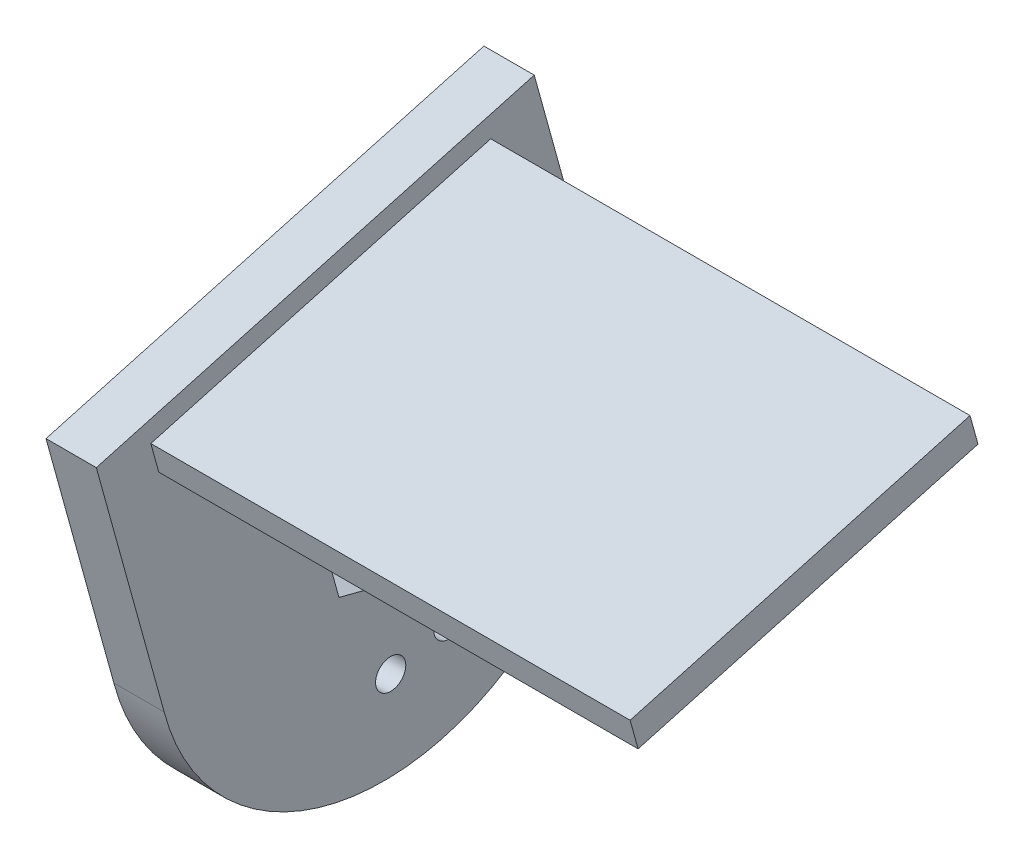
SolidWorks part; units mm, degrees
ref_plane "Front Plane" through (0, 0, 0) normal (0, 0, 1) x (1, 0, 0)
ref_plane "Top Plane" through (0, 0, 0) normal (0, 1, 0) x (1, 0, 0)
ref_plane "Right Plane" through (0, 0, 0) normal (1, 0, 0) x (0, 0, -1)
sketch "Sketch1" plane through (0, 0, 0) normal (1, 0, 0) x (0, 0, -1)
  circle A0 centre (0, 0) radius 22.57
  dimension "D1" = 45.14
extrude "Boss-Extrude1" add sketch "Sketch1" along normal blind 5
sketch "Sketch3" plane through (5, 0, 0) normal (1, 0, 0) x (0, 0, -1)
  line L0 (21.8337, 5.7178) -> (14.931, 30.7011)
  line L1 (14.931, 30.7011) -> (-28.5749, 18.6807)
  line L2 (-28.5749, 18.6807) -> (-21.8337, -5.7178)
  line L3 (21.8337, 5.7178) -> (-21.8337, -5.7178)
  line L4 (-21.7529, -6.0102) -> (-28.5749, 18.6807) construction
  line L5 (14.931, 30.7011) -> (21.7529, 6.0102) construction
  circle A1 centre (0, 0) radius 22.57 construction
extrude "Boss-Extrude2" add sketch "Sketch3" against normal blind 5
sketch "Sketch4" plane through (0, 0, 0) normal (-1, 0, 0) x (0, 0, 1)
  line L0 (-1.5433, -5.5857) -> (4.0657, -4.1294) construction
  line L1 (4.0657, -4.1294) -> (5.609, 1.4563) construction
  line L2 (5.609, 1.4563) -> (1.5433, 5.5857) construction
  line L3 (1.5433, 5.5857) -> (-4.0657, 4.1294) construction
  line L4 (-4.0657, 4.1294) -> (-5.609, -1.4563) construction
  line L5 (-5.609, -1.4563) -> (-1.5433, -5.5857) construction
  line L6 (-1.5433, -5.5857) -> (4.0657, -4.1294) construction
  line L7 (4.4708, -4.5408) -> (6.1678, 1.6014)
  line L8 (6.1678, 1.6014) -> (1.6971, 6.1422)
  line L9 (1.6971, 6.1422) -> (-4.4708, 4.5408)
  line L10 (-4.4708, 4.5408) -> (-6.1678, -1.6014)
  line L11 (-6.1678, -1.6014) -> (-1.6971, -6.1422)
  line L12 (-1.6971, -6.1422) -> (4.4708, -4.5408)
  circle A0 centre (0, 0) radius 5.0186 construction
  circle A1 centre (0, 0) radius 5.5186 construction
  dimension "D1" = 0.5
  dimension "D2" = 0
extrude "Cut-Extrude2" cut sketch "Sketch4" against normal blind 5
sketch "Sketch5" plane through (5, 0, 0) normal (1, 0, 0) x (0, 0, -1)
  circle A0 centre (0.6693, -13.6872) radius 1.5
  circle A1 centre (6.4526, -12.0893) radius 1.5
extrude "Cut-Extrude3" cut sketch "Sketch5" against normal blind 5
sketch "Sketch6" plane through (5, 0, 0) normal (1, 0, 0) x (0, 0, -1)
  line L0 (10.6442, 27.4418) -> (-23.2228, 18.0845)
  line L5 (-23.2228, 18.0845) -> (-22.4063, 15.1292)
  line L6 (-22.4063, 15.1292) -> (11.4607, 24.4865)
  line L7 (11.4607, 24.4865) -> (-22.4063, 15.1292) construction
  line L8 (10.6442, 27.4418) -> (11.4607, 24.4865) construction
  line L9 (11.4607, 24.4865) -> (10.6442, 27.4418)
extrude "Boss-Extrude3" add sketch "Sketch6" along normal up to surface (47.62 mm away)
sketch "Sketch7" plane through (52.62, 0, 0) normal (1, 0, 0) x (0, 0, -1)
  line L0 (11.3992, 24.5214) -> (10.6093, 27.3803)
  line L1 (10.6093, 27.3803) -> (-23.1613, 18.0496)
  line L2 (-23.1613, 18.0496) -> (-22.3714, 15.1907)
  line L3 (-22.3714, 15.1907) -> (11.3992, 24.5214)
  line L4 (11.4607, 24.4865) -> (-22.4063, 15.1292) construction
  line L5 (-23.2228, 18.0845) -> (10.6442, 27.4418) construction
  line L7 (-22.4063, 15.1292) -> (-23.2228, 18.0845) construction
  line L8 (10.6442, 27.4418) -> (11.4607, 24.4865) construction
  line L9 (11.4607, 24.4865) -> (10.6442, 27.4418)
  line L10 (10.6442, 27.4418) -> (-23.2228, 18.0845)
  line L11 (-23.2228, 18.0845) -> (-22.4063, 15.1292)
  line L12 (-22.4063, 15.1292) -> (11.4607, 24.4865)
  dimension "D1" = 0.05
  dimension "0" = 0.05
  dimension "D3" = 0.05
  dimension "D4" = 0.05
extrude "Cut-Extrude5" cut sketch "Sketch7" against normal up to surface (47.62 mm away) up to face at (5, -13.6872, -2.1693)
